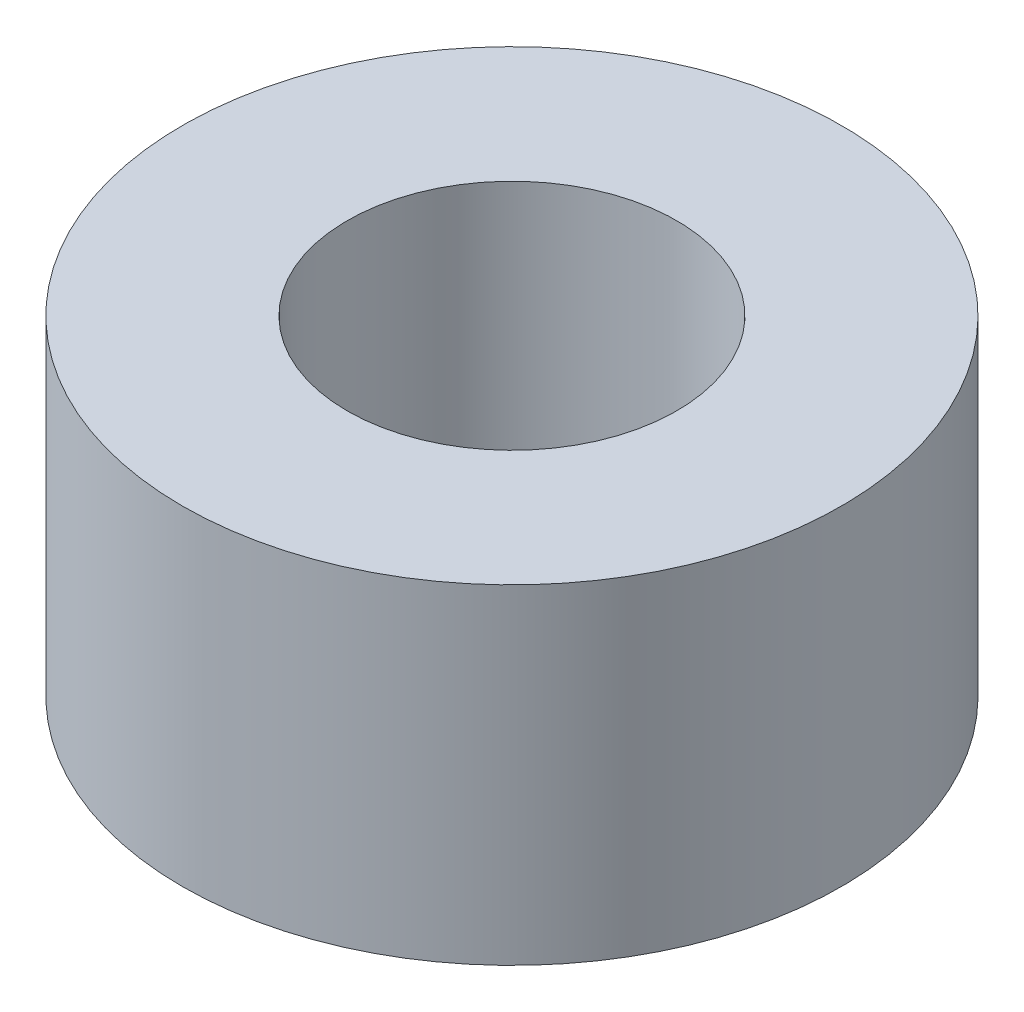
SolidWorks part; units mm, degrees
ref_plane "Front Plane" through (0, 0, 0) normal (0, 0, 1) x (1, 0, 0)
ref_plane "Top Plane" through (0, 0, 0) normal (0, 1, 0) x (1, 0, 0)
ref_plane "Right Plane" through (0, 0, 0) normal (1, 0, 0) x (0, 0, -1)
sketch "Sketch1" plane through (0, 0, 0) normal (0, 1, 0) x (1, 0, 0)
  circle A0 centre (0, 0) radius 2.54
  circle A1 centre (0, 0) radius 5.08
  dimension "D1" = 5.08
  dimension "D2" = 2.54
extrude "Boss-Extrude1" add sketch "Sketch1" along normal blind 5.08
equation "\"glass pane length\" = 14.125"
equation "\"glass pane width\" = 10.1875"
equation "\"glass pane wall width\" = 3/4"
equation "\"glass lip\" = 1/4"
equation "\"bolt diameter\" = 0.2"
equation "\"stepper body width\" = 2.22"
equation "\"stepper mount offset\" = 0.19"
equation "\"stepper mount diameter\" = 0.19"
equation "\"y axis stepper wall bracket thickness\" = 1"
equation "\"y axis stepper wall mount side offset\" = 1/2"
equation "\"y axis stepper wall mount top offset\" = 1/2"
equation "\"y axis stepper wall width\" = \"stepper body width\" + 1                  "
equation "\"thin metal\" = 0.12"
equation "\"thick metal\" = 0.25"
equation "\"D1@Sketch1\"=\"bolt diameter\""
equation "\"stepper spacer thickness\" = 0.2"
equation "\"y axis stepper wall height off base\" = 8"
equation "\"D1@Boss-Extrude1\" = \"stepper spacer thickness\""
